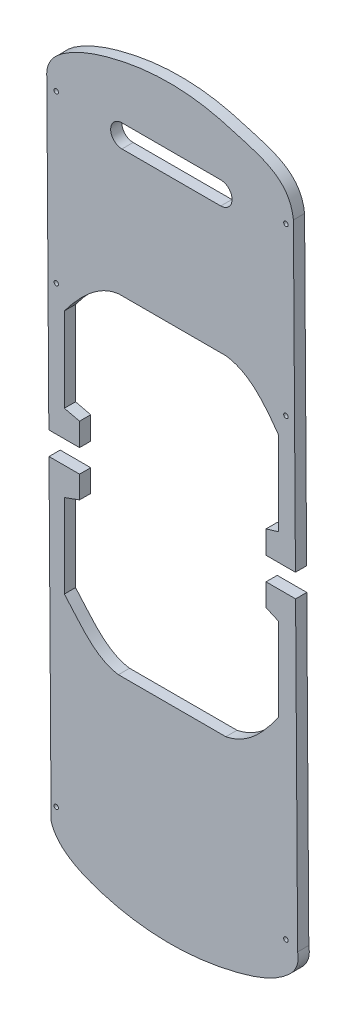
SolidWorks part; units mm, degrees
ref_plane "Front Plane" through (0, 0, 0) normal (0, 0, 1) x (1, 0, 0)
ref_plane "Top Plane" through (0, 0, 0) normal (0, 1, 0) x (1, 0, 0)
ref_plane "Right Plane" through (0, 0, 0) normal (1, 0, 0) x (0, 0, -1)
sketch "Reference" plane through (0, 0, 0) normal (0, 0, 1) x (1, 0, 0)
  line L0 (-348.8502, -49.1843) -> (141.8928, -49.1843) construction
  line L1 (-110.0526, 0) -> (105.8474, 0) construction
  point P8 (0, 0)
  point P14 (0, 0)
  point P18 (0, 0)
  dimension "D1" = 215.9
sketch "Outer Cut" plane through (0, 0, 0) normal (0, 0, 1) x (1, 0, 0)
  line L0 (-113.6488, 299.1498) -> (-109.8162, -275.0931)
  line L1 (110.7741, -266.2189) -> (107.0008, 299.1498)
  spline S0 degree 3 poles (-109.8162, -275.0931) (-106.6072, -285.7225) (-92.2302, -298.1286) (-66.1715, -308.1255) (-35.4902, -315.6804) (7.3493, -318.5293) (55.2594, -311.1992) (97.2761, -296.3858) (112.8708, -277.1332) (110.7741, -266.2189) knots 0 0 0 0 0.122426 0.216064 0.327166 0.494334 0.717397 0.899565 1 1 1 1
  spline S1 degree 3 poles (-113.6488, 299.1498) (-114.9244, 313.1979) (-94.8498, 330.3934) (-61.01, 342.6225) (-18.9188, 351.1769) (23.6095, 349.7539) (71.6874, 335.6922) (104.0964, 325.362) (107.0008, 299.1498) knots 0 0 0 0 0.141862 0.279973 0.416533 0.634994 0.759519 1 1 1 1
sketch "Handle" plane through (0, 0, 0) normal (0, 0, 1) x (1, 0, 0)
  line L0 (-46.401, 287.5517) -> (41.9817, 287.5517) construction
  line L1 (-46.401, 297.6663) -> (41.9817, 297.6663)
  line L2 (-46.401, 277.437) -> (41.9817, 277.437)
  arc A0 (-46.401, 297.6663) -> (-46.401, 277.437) centre (-46.401, 287.5517) ccw
  arc A1 (41.9817, 277.437) -> (41.9817, 297.6663) centre (41.9817, 287.5517) ccw
  point P2 (-2.2096, 287.5517)
  point P7 (0, 0)
sketch "Holes" plane through (0, 0, 0) normal (0, 0, 1) x (1, 0, 0)
  circle A0 centre (100.286, 292.776) radius 2
  circle A1 centre (-105.2342, 292.776) radius 2
  circle A2 centre (-105.2342, 144.0131) radius 2
  circle A3 centre (100.286, 144.0131) radius 2
  circle A4 centre (-105.2342, -261.8133) radius 2
  circle A5 centre (100.286, -261.8173) radius 2
  point P2 (103.8596, -264.8133)
  point P5 (0, 0)
  point P12 (0, 0)
  point P13 (0, 0)
  point P14 (103.982, -264.8133)
  point P17 (100.286, -264.8133)
  point P18 (103.9816, -261.8173)
  point P19 (0, 0)
  point P20 (0, 0)
  point P21 (0, 0)
  point P22 (0, 0)
  point P23 (0, 0)
  point P24 (0, 0)
sketch "Wheel Hole" plane through (0, 0, 0) normal (0, 0, 1) x (1, 0, 0)
  line L0 (-49.5789, 163.6609) -> (46.5388, 163.6609)
  line L1 (93.454, 126.2162) -> (93.454, 50.7479)
  line L2 (-97.9326, 126.2162) -> (-97.9326, 50.7373)
  line L3 (-84.37, 47.4941) -> (-84.37, -13.5377)
  line L4 (82.5093, 47.4941) -> (82.5093, -13.5377)
  line L5 (-97.9326, -18.434) -> (-97.9326, -93.2519)
  line L6 (-49.5789, -131.5631) -> (46.5388, -131.5631)
  line L7 (93.454, -18.434) -> (93.454, -93.2519)
  line L8 (82.5093, 47.4941) -> (93.454, 50.7479)
  line L9 (82.5093, -13.5377) -> (93.454, -18.434)
  line L10 (-97.9326, -18.434) -> (-84.37, -13.5377)
  line L11 (-97.9326, 50.7373) -> (-84.37, 47.4941)
  spline S0 degree 3 poles (93.454, -93.2519) (81.8989, -109.4101) (67.308, -127.5224) (46.5388, -131.5631) knots 0 0 0 0 1 1 1 1
  spline S1 degree 3 poles (-49.5789, -131.5631) (-71.5326, -128.3717) (-84.3062, -107.7885) (-97.9326, -93.2519) knots 0 0 0 0 1 1 1 1
  spline S2 degree 3 poles (46.5388, 163.6609) (68.3726, 160.8689) (81.8047, 142.5255) (93.454, 126.2162) knots 0 0 0 0 1 1 1 1
  spline S3 degree 3 poles (-49.5789, 163.6609) (-60.5616, 162.1199) (-78.2274, 150.2639) (-91.833, 134.4131) (-97.9326, 126.2162) knots 0 0 0 0 0.510558 1 1 1 1
  point P21 (93.454, -18.434)
extrude "Outer Cut Extrude" add sketch "Outer Cut" along normal blind 10
extrude "Handle Cut" cut sketch "Handle" along direction (0, 0, 1) on the side of the normal up to surface (10 mm away)
extrude "Holes Cut" cut sketch "Holes" along direction (0, 0, 1) on the side of the normal up to surface (10 mm away)
extrude "Wheel Hole Cut" cut sketch "Wheel Hole" along normal up to surface (10 mm away) up to face at (-103.2342, 144.0131, 10)
sketch "Sketch7" plane through (0, 0, 0) normal (0, 0, 1) x (1, 0, 0)
  line L0 (-113.6488, 299.1498) -> (-109.8162, -275.0931) construction
  line L1 (-111.8323, 26.9857) -> (108.9542, 26.9857)
  line L2 (-111.8323, 26.9857) -> (-111.8323, 6.4625)
  line L3 (-111.8323, 6.4625) -> (108.9542, 6.4625)
  line L4 (108.9542, 26.9857) -> (108.9542, 6.4625)
  line L5 (110.7741, -266.2189) -> (107.0008, 299.1498) construction
extrude "Seperate For Cutter" cut sketch "Sketch7" along normal up to surface (10 mm away) up to face at (-103.2342, 144.0131, 10)
